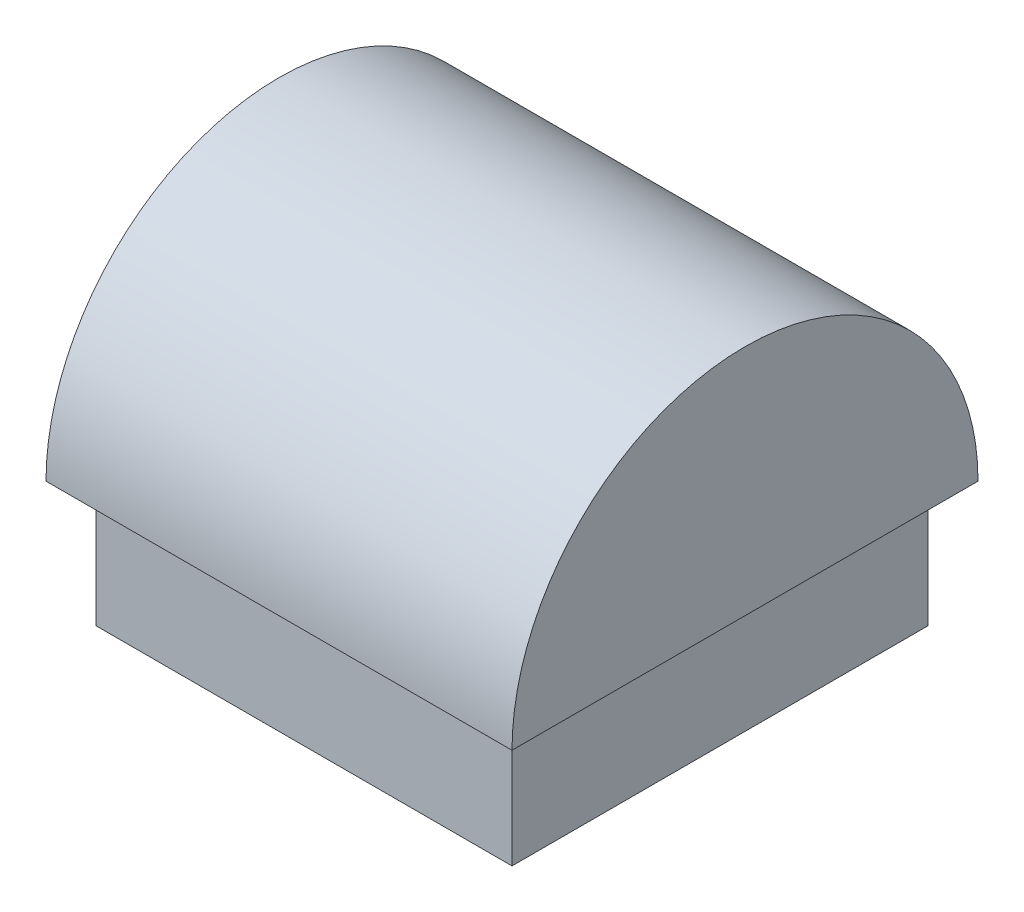
SolidWorks part; units mm, degrees
material "PPE"
ref_plane "Front Plane" through (0, 0, 0) normal (0, 0, 1) x (1, 0, 0)
ref_plane "Top Plane" through (0, 0, 0) normal (0, 1, 0) x (1, 0, 0)
ref_plane "Right Plane" through (0, 0, 0) normal (1, 0, 0) x (0, 0, -1)
sketch "Sketch1" plane through (0, 0, 0) normal (0, 1, 0) x (1, 0, 0)
  line L1 (-10.541, -10.541) -> (10.541, -10.541)
  line L2 (-10.541, -10.541) -> (-10.541, 10.541)
  line L3 (-10.541, 10.541) -> (10.541, 10.541)
  line L4 (10.541, -10.541) -> (10.541, 10.541)
  line L5 (-10.541, -10.541) -> (10.541, 10.541) construction
  line L6 (-10.541, 10.541) -> (10.541, -10.541) construction
  line L11 (-7.366, -7.366) -> (7.366, 7.366) construction
  line L12 (-7.366, 7.366) -> (7.366, -7.366) construction
  point P0 (0, 0)
  point P6 (0, 0)
  dimension "D1" = 21.082
  dimension "D2" = 21.082
extrude "Boss-Extrude1" add sketch "Sketch1" along normal blind 6.35
sketch "Sketch2" plane through (0, 6.35, 0) normal (0, 1, 0) x (1, 0, 0)
  line L1 (-11.43, -11.43) -> (11.43, -11.43)
  line L2 (-11.43, -11.43) -> (-11.43, 11.43)
  line L3 (-11.43, 11.43) -> (11.43, 11.43)
  line L4 (11.43, -11.43) -> (11.43, 11.43)
  line L5 (-11.43, -11.43) -> (11.43, 11.43) construction
  line L6 (-11.43, 11.43) -> (11.43, -11.43) construction
  point P0 (0, 0)
  dimension "D1" = 22.86
  dimension "D2" = 22.86
sketch "Sketch3" plane through (0, 0, 0) normal (1, 0, 0) x (0, 0, -1)
  line L6 (-11.811, 6.35) -> (11.811, 6.35)
  line L7 (10.541, 6.35) -> (-10.541, 6.35) construction
  arc A0 (11.811, 6.35) -> (-11.811, 6.35) centre (0, 6.35) ccw
  point P3 (0, 6.35)
  dimension "D1" = 23.622
extrude "Boss-Extrude2" add sketch "Sketch3" along normal mid plane 23.622
scale "Scale1" scale about centroid uniform scaling yes scale factor 1.02
